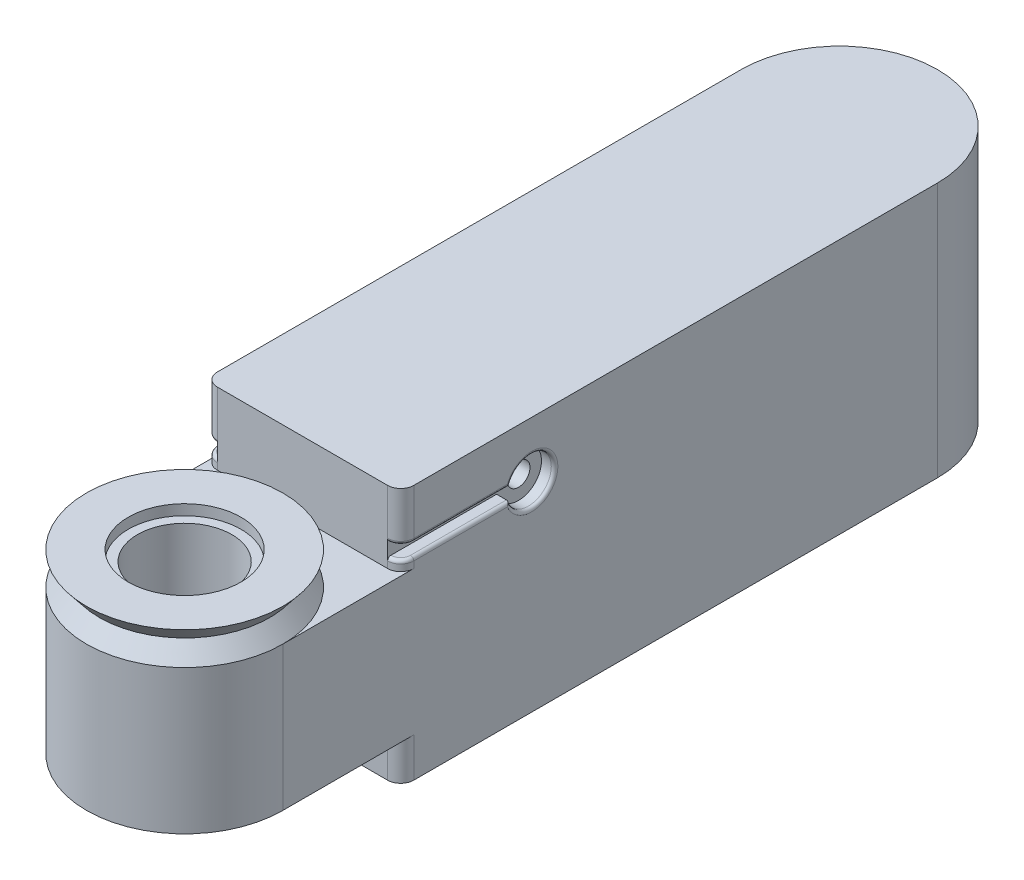
SolidWorks part; units mm, degrees
ref_plane "정면" through (0, 0, 0) normal (0, 0, 1) x (1, 0, 0)
ref_plane "윗면" through (0, 0, 0) normal (0, 1, 0) x (1, 0, 0)
ref_plane "우측면" through (0, 0, 0) normal (1, 0, 0) x (0, 0, -1)
sketch "스케치1" plane through (0, 0, 0) normal (0, 1, 0) x (1, 0, 0)
  line L0 (0, 0) -> (0, 50) construction
  line L1 (-7.5, 0) -> (-7.5, 50)
  line L2 (7.5, 0) -> (7.5, 50)
  arc A0 (-7.5, 0) -> (7.5, 0) centre (0, 0) ccw
  arc A1 (7.5, 50) -> (-7.5, 50) centre (0, 50) ccw
  point P3 (0, 25)
  dimension "D1" = 7.5
  dimension "D2" = 50
extrude "보스-돌출1" add sketch "스케치1" along normal blind 11
sketch "스케치2" plane through (0, 0, 0) normal (0, 0, 1) x (1, 0, 0)
  line L0 (-7.5, 11) -> (0, 11)
  line L1 (7.5, 11) -> (-7.5, 11) construction
  line L2 (0, 11) -> (0, 13.5)
  line L3 (0, -55) -> (0, 55) construction
  line L4 (0, 13.5) -> (-7.5, 13.5)
  line L5 (-7.5, 13.5) -> (-6.5, 12.25)
  line L6 (-6.5, 12.25) -> (-7.5, 11)
  line L7 (0, 13.5) -> (0, 11) construction
  point P13 (0, 12.25)
  dimension "D1" = 2.5
  dimension "D2" = 6.5
revolve "회전1" add sketch "스케치2" angle 360 about L7
sketch "스케치3" plane through (0, 0, 0) normal (0, -1, 0) x (1, 0, 0)
  line L0 (-7.5, -50) -> (-7.5, -9)
  line L2 (7.5, -50) -> (7.5, -9)
  line L3 (-7.5, -9) -> (7.5, -9)
  arc A0 (-7.5, -50) -> (7.5, -50) centre (0, -50) ccw
  arc A1 (-7.5, -50) -> (7.5, -50) centre (0, -50) ccw construction
  dimension "D1" = 9
extrude "보스-돌출2" add sketch "스케치3" along normal blind 3 and the other way offset from surface (16.5 mm away) 5.5 other way up to face at (0, 11, -28.75)
fillet "필렛1" radius 1 4 edges at (-7.5, 13.75, -9) (7.5, 13.75, -9) (7.5, -1.5, -9) (-7.5, -1.5, -9)
sketch "스케치6" plane through (0, 0, -9) normal (0, 0, 1) x (1, 0, 0)
  line L1 (-7.5, 12.75) -> (-6.5, 12.75)
  line L2 (-7.5, 12.75) -> (-7.5, 11.75)
  line L3 (-7.5, 11.75) -> (-6.5, 11.75)
  line L4 (-6.5, 12.75) -> (-6.5, 11.75)
  line L6 (7.5, 11.75) -> (6.5, 11.75)
  line L7 (7.5, 11.75) -> (7.5, 12.75)
  line L8 (7.5, 12.75) -> (6.5, 12.75)
  line L9 (6.5, 11.75) -> (6.5, 12.75)
  line L10 (7.5, 16.5) -> (7.5, 11) construction
  line L11 (-7.5, 11) -> (-7.5, 16.5) construction
  line L12 (6.5, 12.25) -> (-6.5, 12.25) construction
  point P15 (-7.5, 12.25)
  point P16 (7.5, 12.25)
  dimension "D1" = 1
  dimension "D2" = 1
  dimension "D3" = 1
  dimension "D4" = 1
extrude "컷-돌출3" cut sketch "스케치6" against normal blind 10
sketch "스케치8" plane through (-7.5, 0, 0) normal (-1, 0, 0) x (0, 0, 1)
  line L1 (-19, 11.75) -> (-10, 11.75) construction
  line L2 (-19, 12.75) -> (-9, 12.75) construction
  circle A0 centre (-19, 12.25) radius 0.5
extrude "컷-돌출4" cut sketch "스케치8" against normal up to surface (15 mm away) up to face at (7.5, 8.1667, -16.5)
sketch "스케치9" plane through (-7.5, 0, 0) normal (-1, 0, 0) x (0, 0, 1)
  circle A0 centre (-19, 12.25) radius 1.5
  dimension "D1" = 3
extrude "컷-돌출5" cut sketch "스케치9" against normal up to surface (1 mm away) up to face at (-6.5, 12.25, -13.875)
sketch "스케치10" plane through (7.5, 0, 0) normal (1, 0, 0) x (0, 0, -1)
  circle A0 centre (19, 12.25) radius 1.75
  dimension "D1" = 3.5
extrude "컷-돌출6" cut sketch "스케치10" against normal up to surface (1 mm away) up to face at (6.5, 12.25, -13.875)
fillet "필렛2" radius 0.25 10 edges at (-7.2071, 11.75, -9.2929) (-7.2071, 12.75, -9.2929) (7.2071, 11.75, -9.2929) (7.2071, 12.75, -9.2929) (-7.5, 12.25, -20.5) (-7.5, 11.75, -13.7929) (-7.5, 12.75, -13.7929) (7.5, 12.25, -20.75) (7.5, 11.75, -13.6615) (7.5, 12.75, -13.6615)
sketch "스케치11" plane through (0, 13.5, 0) normal (0, 1, 0) x (1, 0, 0)
  circle A0 centre (0, 0) radius 2
  dimension "D1" = 4
extrude "컷-돌출7" cut sketch "스케치11" against normal up to surface (13.5 mm away) up to face at (0, 0, -5.0143)
sketch "스케치13" plane through (0, 13.5, 0) normal (0, 1, 0) x (1, 0, 0)
  circle A0 centre (0, 0) radius 3.6
  dimension "D1" = 7.2
extrude "컷-돌출8" cut sketch "스케치13" against normal up to surface (13.5 mm away) up to face at (0, 0, 2)
sketch "스케치14" plane through (0, 13.5, 0) normal (0, 1, 0) x (1, 0, 0)
  circle A0 centre (0, 0) radius 4.3
  dimension "D1" = 8.6
sketch "스케치15" plane through (0, 0, 0) normal (0, -1, 0) x (-1, 0, 0)
  circle A0 centre (0, 0) radius 4.3
  dimension "D1" = 8.6
extrude "컷-돌출9" cut sketch "스케치14" against normal blind 0.8
extrude "컷-돌출10" cut sketch "스케치15" against normal blind 0.8
sketch "스케치16" plane through (6.5, 0, 0) normal (1, 0, 0) x (0, 0, -1)
  circle A0 centre (19, 12.25) radius 0.875
  dimension "D1" = 1.75
extrude "컷-돌출11" cut sketch "스케치16" against normal up to surface (13 mm away) up to face at (-6.5, 12.25, -12.4137)
